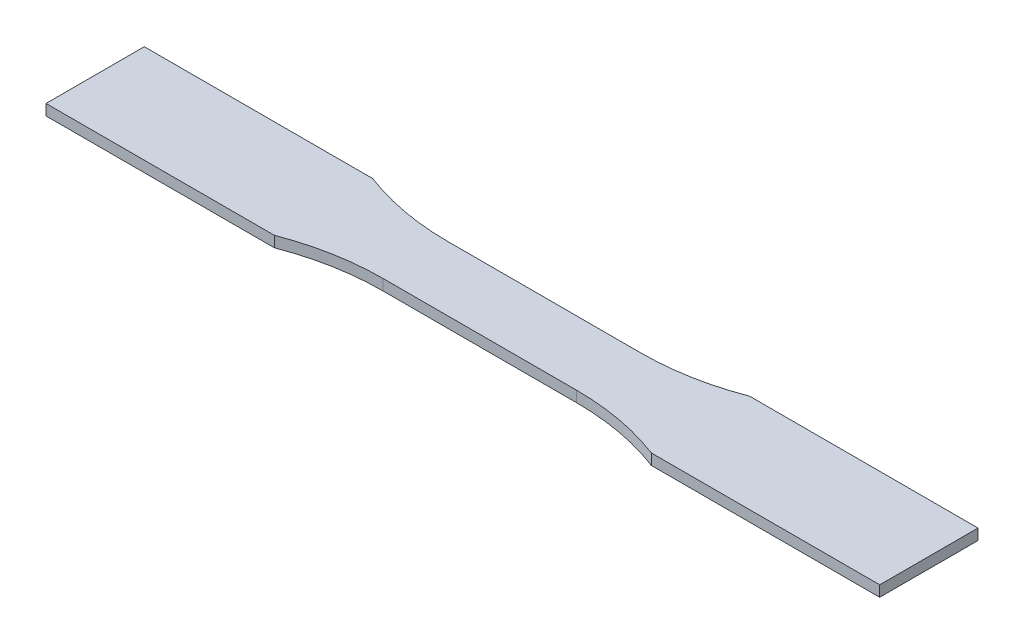
SolidWorks part; units mm, degrees
material "PET"
ref_plane "Alzado" through (0, 0, 0) normal (0, 0, 1) x (1, 0, 0)
ref_plane "Planta" through (0, 0, 0) normal (0, 1, 0) x (1, 0, 0)
ref_plane "Vista lateral" through (0, 0, 0) normal (1, 0, 0) x (0, 0, -1)
sketch "Croquis1" plane through (0, 0, 0) normal (0, 1, 0) x (1, 0, 0)
  line L1 (123, -14.5) -> (-123, -14.5)
  line L2 (123, -14.5) -> (123, 14.5)
  line L3 (123, 14.5) -> (-123, 14.5)
  line L4 (-123, -14.5) -> (-123, 14.5)
  line L5 (123, -14.5) -> (-123, 14.5) construction
  line L6 (123, 14.5) -> (-123, -14.5) construction
  line L7 (28.5, -9.5) -> (-28.5, -9.5)
  line L8 (28.5, -9.5) -> (28.5, 9.5)
  line L9 (28.5, 9.5) -> (-28.5, 9.5)
  line L10 (-28.5, -9.5) -> (-28.5, 9.5)
  line L11 (28.5, -9.5) -> (-28.5, 9.5) construction
  line L12 (28.5, 9.5) -> (-28.5, -9.5) construction
  arc A0 (-55.6109, 14.5) -> (-28.5, 9.5) centre (-28.5, 85.5) ccw
  arc A3 (55.6109, -14.5) -> (28.5, -9.5) centre (28.5, -85.5) ccw
  arc A4 (28.5, 9.5) -> (55.6109, 14.5) centre (28.5, 85.5) ccw
  arc A6 (-28.5, -9.5) -> (-55.6109, -14.5) centre (-28.5, -85.5) ccw
  point P0 (0, 0)
  point P6 (0, 0)
  dimension "D5" = 152
  dimension "D1" = 29
  dimension "D2" = 246
  dimension "D3" = 19
  dimension "D4" = 57
extrude "Saliente-Extruir1" add sketch "Croquis1" along normal mid plane 3.2 contours A6 L10 A0 L3 L4 L1 | A4 L8 A3 L1 L2 L3 | L10 L7 L8 L9
sketch "Croquis2" plane through (0, 1.6, 0) normal (0, 1, 0) x (1, 0, 0)
  line L0 (-57.5, 14.5) -> (-57.5, -14.5)
  line L1 (-55.6109, 14.5) -> (-123, 14.5) construction
  line L2 (-55.6109, -14.5) -> (-123, -14.5) construction
  line L3 (57.5, 14.5) -> (57.5, -14.5)
  line L4 (123, 14.5) -> (55.6109, 14.5) construction
  line L5 (123, -14.5) -> (55.6109, -14.5) construction
  line L6 (57.5, 0) -> (-57.5, 0) construction
  point P14 (0, 0)
  dimension "D1" = 115
